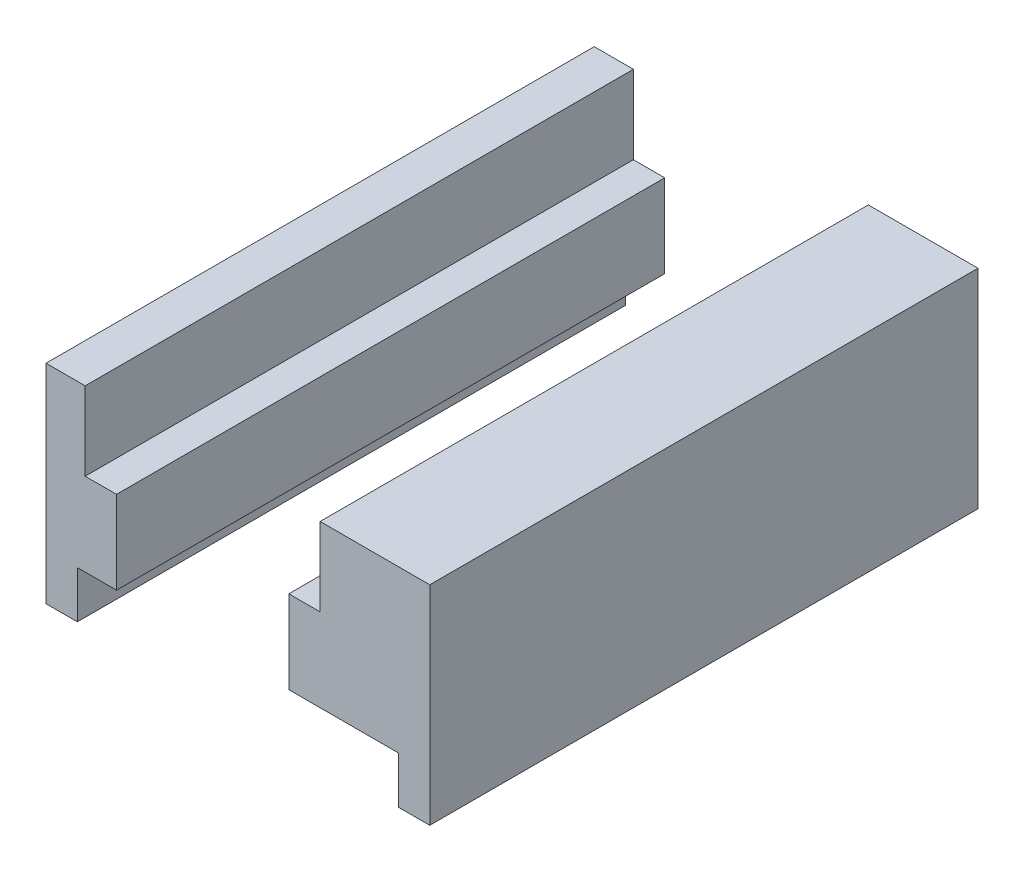
SolidWorks part; units mm, degrees
ref_plane "Front Plane" through (0, 0, 0) normal (0, 0, 1) x (1, 0, 0)
ref_plane "Top Plane" through (0, 0, 0) normal (0, 1, 0) x (1, 0, 0)
ref_plane "Right Plane" through (0, 0, 0) normal (1, 0, 0) x (0, 0, -1)
sketch "Sketch1" plane through (0, 0, 0) normal (0, 1, 0) x (1, 0, 0)
  line L0 (-10.25, 0) -> (10.25, 0)
  dimension "D1" = 20.5
sketch "Sketch2" plane through (0, 0, 0) normal (0, 0, 1) x (1, 0, 0)
  line L11 (-10.25, 0) -> (10.25, 0) construction
  line L16 (0, -0.5712) -> (0, 1.3971) construction
  line L33 (10.25, 0) -> (10.25, 3)
  line L34 (10.25, 3) -> (3.25, 3)
  line L35 (3.25, 3) -> (3.25, 8.3)
  line L36 (3.25, 8.3) -> (5.25, 8.3)
  line L37 (5.25, 8.3) -> (5.25, 13.3)
  line L38 (-7.75, 8.3) -> (-7.75, 3)
  line L39 (-7.75, 3) -> (-10.25, 3)
  line L40 (-7.75, 8.3) -> (-9.75, 8.3)
  line L41 (-9.75, 8.3) -> (-9.75, 13.3)
  line L42 (-9.75, 13.3) -> (-12.25, 13.3)
  line L43 (-10.25, 3) -> (-10.25, 0)
  line L44 (-12.25, 0) -> (-10.25, 0)
  line L45 (5.25, 13.3) -> (12.25, 13.3)
  line L46 (12.25, 13.3) -> (12.25, 0)
  line L47 (-12.25, 13.3) -> (-12.25, 0)
  line L52 (12.25, 0) -> (10.25, 0)
  point P24 (-9.75, 10.8)
  point P25 (0, 0)
  dimension "D2" = 5
  dimension "D3" = 8.3
  dimension "D6" = 2.5
  dimension "D7" = 3
  dimension "D8" = 8.3
  dimension "D10" = 2
  dimension "D11" = 2
  dimension "D12" = 2
  dimension "D13" = 7
  dimension "D14" = 5
  dimension "D15" = 3
  dimension "D16" = 2
extrude "Boss-Extrude3" add sketch "Sketch2" along normal blind 35
